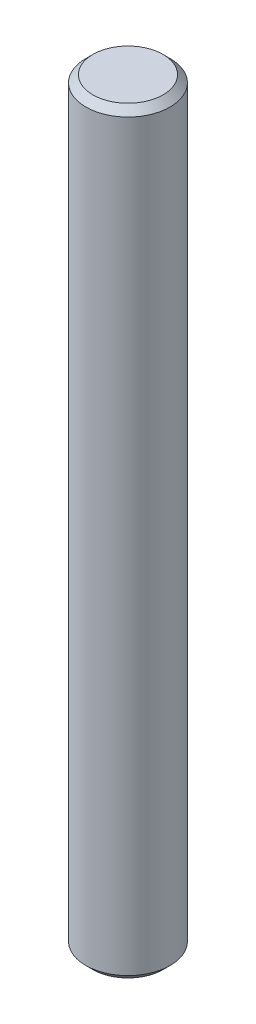
SolidWorks part; units mm, degrees
material "Aço carbono simples"
ref_plane "Front" through (0, 0, 0) normal (0, 0, 1) x (1, 0, 0)
ref_plane "Top" through (0, 0, 0) normal (0, 1, 0) x (1, 0, 0)
ref_plane "Right" through (0, 0, 0) normal (1, 0, 0) x (0, 0, -1)
sketch "Esboço2" plane through (0, 0, 0) normal (0, 1, 0) x (1, 0, 0)
  circle A0 centre (0, 0) radius 3
extrude "Ressalto-extrusão1" add sketch "Esboço2" along normal mid plane 54
chamfer "Chanfro1" distance 0.5 angle 45 2 edges at (0, -27, 3) (0, 27, 3)
